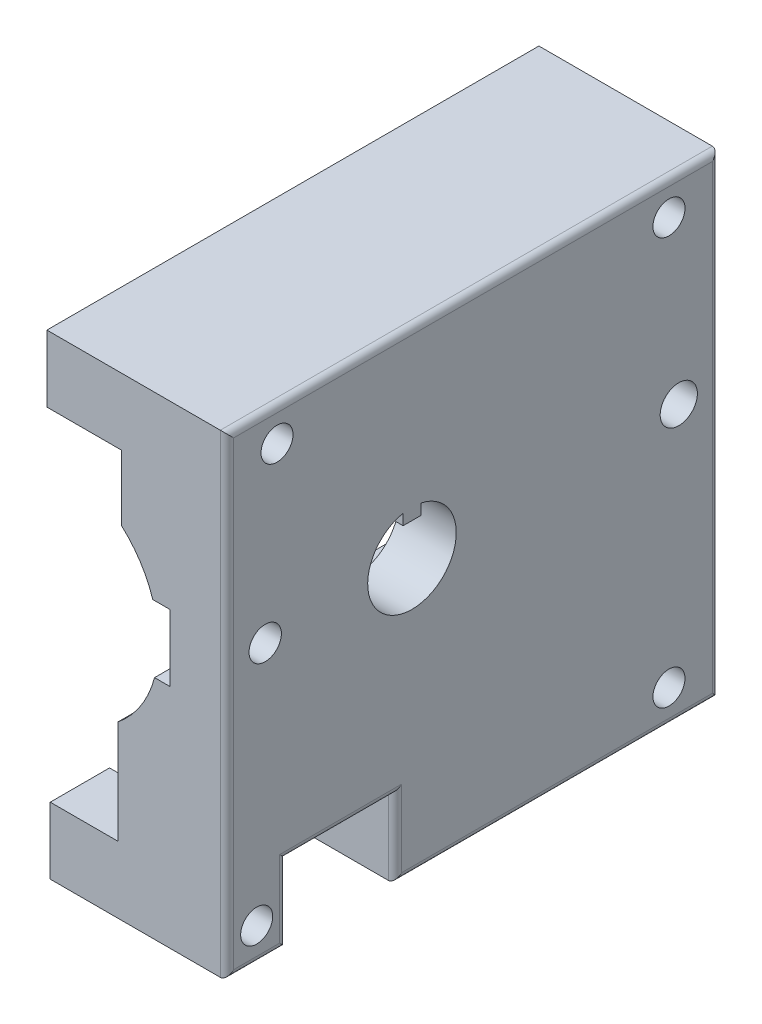
SolidWorks part; units mm, degrees
ref_plane "Front" through (0, 0, 0) normal (0, 0, 1) x (1, 0, 0)
ref_plane "Top" through (0, 0, 0) normal (0, 1, 0) x (1, 0, 0)
ref_plane "Right" through (0, 0, 0) normal (1, 0, 0) x (0, 0, -1)
sketch "Profile" plane through (0, 0, 0) normal (0, 0, 1) x (1, 0, 0)
  line L0 (-6.0107, -43.6279) -> (-6.0107, -33.6279)
  line L1 (-6.0107, -43.6279) -> (20.4893, -43.6279)
  line L2 (-6.5107, 17.4121) -> (-6.5107, 27.4121)
  line L3 (-6.5107, 27.4121) -> (20.4893, 27.4121)
  line L4 (20.4893, -43.6279) -> (20.4893, 27.4121)
  line L5 (-6.0107, -33.6279) -> (4.1393, -33.6279)
  line L6 (4.1393, -33.6279) -> (4.1393, -18.1379)
  line L7 (9.6313, -9.6379) -> (11.9493, -9.6379)
  line L8 (11.9493, -9.6379) -> (11.9493, 0.3621)
  line L9 (9.3593, 0.3621) -> (11.9493, 0.3621)
  line L10 (4.6393, 17.4121) -> (4.6393, 7.6371)
  line L11 (4.6393, 17.4121) -> (-6.5107, 17.4121)
  arc A0 (9.3593, 0.3621) -> (4.6393, 7.6371) centre (-6.1482, -4.5305) ccw
  arc A1 (4.1393, -18.1379) -> (9.6313, -9.6379) centre (-6.0948, -5.5013) ccw
  dimension "D14" = 16.261
  dimension "D17" = 16.261
  dimension "D2" = 10
  dimension "D3" = 2.59
  dimension "D4" = 2.318
  dimension "D5" = 9.775
  dimension "D6" = 11.15
  dimension "D7" = 15.49
  dimension "D8" = 10.15
  dimension "D9" = 10
  dimension "D10" = 26.5
  dimension "D11" = 71.04
  dimension "D12" = 27
  dimension "D13" = 10
  dimension "D15" = 23.99
  dimension "D16" = 5.492
extrude "ProfileExtrude" add sketch "Profile" along normal blind 73.76
sketch "HoseWindow" plane through (20.4893, 0, 0) normal (1, 0, 0) x (0, 0, -1)
  line L0 (-73.76, -43.6279) -> (0, -43.6279) construction
  line L1 (-64.87, -43.6279) -> (-48.58, -43.6279)
  line L2 (-64.87, -43.6279) -> (-64.87, -32.1279)
  line L3 (-64.87, -32.1279) -> (-48.58, -32.1279)
  line L4 (-48.58, -43.6279) -> (-48.58, -32.1279)
  line L5 (-73.76, -43.6279) -> (-73.76, 27.4121) construction
  dimension "D1" = 16.29
  dimension "D2" = 11.5
  dimension "D3" = 8.89
extrude "HoseWindowCut" cut sketch "HoseWindow" against normal through all
sketch "CageScrews" plane through (20.4893, 0, 0) normal (1, 0, 0) x (0, 0, -1)
  line L0 (-73.76, 27.4121) -> (0, 27.4121) construction
  line L1 (-73.76, -43.6279) -> (-73.76, 27.4121) construction
  line L2 (0, -43.6279) -> (0, 27.4121) construction
  line L3 (-48.58, -43.6279) -> (0, -43.6279) construction
  line L4 (-73.76, -43.6279) -> (-64.87, -43.6279) construction
  circle A0 centre (-66.26, 22.4121) radius 2.4
  circle A1 centre (-7.5, 22.4121) radius 2.4
  circle A2 centre (-7.5, -38.6279) radius 2.4
  circle A3 centre (-69.31, -38.6279) radius 2.4
  dimension "D1" = 4.8
  dimension "D2" = 4.8
  dimension "D3" = 4.8
  dimension "D4" = 4.8
  dimension "D5" = 5
  dimension "D6" = 7.5
  dimension "D7" = 7.5
  dimension "D8" = 5
  dimension "D9" = 5
  dimension "D10" = 7.5
  dimension "D11" = 5
  dimension "D12" = 4.45
extrude "CageScrewsCut" cut sketch "CageScrews" against normal through all
sketch "AxleHole" plane through (20.4893, 0, 0) normal (1, 0, 0) x (0, 0, -1)
  line L0 (-46.03, 2.3073) -> (-46.03, -9.2169) construction
  line L1 (-44.699, 2.3073) -> (-47.361, 2.3073)
  line L2 (-47.361, 2.3073) -> (-47.361, 3.9263)
  line L3 (-44.699, 2.3073) -> (-44.699, 3.9263)
  line L4 (-48.58, -43.6279) -> (0, -43.6279) construction
  line L5 (0, -43.6279) -> (0, 27.4121) construction
  arc A0 (-47.361, 3.9263) -> (-44.699, 3.9263) centre (-46.03, -2.5779) ccw
  dimension "D1" = 13.278
  dimension "D2" = 1.619
  dimension "D3" = 1.619
  dimension "D4" = 1.331
  dimension "D5" = 41.05
  dimension "D6" = 46.03
extrude "AxleHoleCut" cut sketch "AxleHole" against normal through all
sketch "SetScrews" plane through (20.4893, 0, 0) normal (1, 0, 0) x (0, 0, -1)
  line L0 (-46.03, -9.2169) -> (-46.03, -2.5779) construction
  circle A0 centre (-68.03, -2.5779) radius 2.4263
  circle A1 centre (-6.03, -2.5779) radius 2.7888
  arc A3 (-47.361, 3.9263) -> (-44.699, 3.9263) centre (-46.03, -2.5779) ccw construction
  dimension "D1" = 22
  dimension "D2" = 40
extrude "SetScrewsCut" cut sketch "SetScrews" against normal through all
fillet "Fillet1" radius 1 8 edges at (20.4893, -37.8779, 64.87) (20.4893, -37.8779, 48.58) (20.4893, -32.1279, 56.725) (20.4893, -43.6279, 69.315) (20.4893, -8.1079, 73.76) (20.4893, -43.6279, 24.29) (20.4893, -8.1079, 0) (20.4893, 27.4121, 36.88)
equation "\"BottomEdge\"=26.5mm"
equation "\"TopEdge\"=27mm"
equation "\"TotalHeight\"=71.04mm"
equation "\"TotalLength\"=73.76mm"
equation "\"Screw Clearance\" = 10mm"
equation "\"TopDepth\"= 11.15mm"
equation "\"BottomDepth\"=10.15mm"
equation "\"TopHeight\"=9.775mm"
equation "\"BottomHeight\"=15.49mm"
equation "\"TopChannelDepth\"=2.59mm"
equation "\"BottomChannelDepth\"=2.318mm"
equation "\"ChannelHeight\"=10mm"
equation "\"ChamberRadius\"=16.261mm"
equation "\"ChanRelHeight\"=23.99mm"
equation "\"ChanRelDepth\"=5.492mm"
equation "\"D2@Profile\"= \"ChannelHeight\""
equation "\"D4@Profile\"= \"BottomChannelDepth\""
equation "\"D3@Profile\"= \"TopChannelDepth\""
equation "\"D5@Profile\"= \"TopHeight\""
equation "\"D7@Profile\"= \"BottomHeight\""
equation "\"D9@Profile\"= \"Screw Clearance\""
equation "\"D13@Profile\"= \"Screw Clearance\""
equation "\"D8@Profile\"= \"BottomDepth\""
equation "\"D6@Profile\"= \"TopDepth\""
equation "\"D10@Profile\"= \"BottomEdge\""
equation "\"D12@Profile\"= \"TopEdge\""
equation "\"D11@Profile\"= \"TotalHeight\""
equation "\"D15@Profile\"= \"ChanRelHeight\""
equation "\"D16@Profile\"= \"ChanRelDepth\""
equation "\"D17@Profile\"= \"ChamberRadius\""
equation "\"D14@Profile\"= \"ChamberRadius\""
equation "\"D1@ProfileExtrude\"= \"TotalLength\""
equation "\"CageScrewDiameter\"=4.8mm"
equation "\"SetScrewDiameter\"=3.5mm"
equation "\"AxleRadius\"=6.639mm"
equation "\"KeyHeight\"=1.619mm"
equation "\"KeyWidth\"=2.662mm"
equation "\"HoseWindowWidth\"=16.29mm"
equation "\"HoseWindowHeight\"=11.5mm"
equation "\"HoseWindow-Edge\"=8.89mm"
equation "\"CageScrew-VerticalEdge\"=5.0mm"
equation "\"CageScrew-HorizontalEdge\"=7.5mm"
equation "\"CageScrew-HoseCornerScrewEdge\"=4.45mm"
equation "\"Axle-BottomEdge\"=41.05mm"
equation "\"Axle-FrontEdge\"=46.03mm"
equation "\"FrontSetScrew-Axel\"=40mm"
equation "\"D1@HoseWindow\"= \"HoseWindowWidth\""
equation "\"D2@HoseWindow\"= \"HoseWindowHeight\""
equation "\"D3@HoseWindow\"= \"HoseWindow-Edge\""
equation "\"D6@CageScrews\"= \"CageScrew-HorizontalEdge\""
equation "\"D7@CageScrews\"= \"CageScrew-HorizontalEdge\""
equation "\"D10@CageScrews\"= \"CageScrew-HorizontalEdge\""
equation "\"D12@CageScrews\"= \"CageScrew-HoseCornerScrewEdge\""
equation "\"D5@CageScrews\"= \"CageScrew-VerticalEdge\""
equation "\"D8@CageScrews\"= \"CageScrew-VerticalEdge\""
equation "\"D11@CageScrews\"= \"CageScrew-VerticalEdge\""
equation "\"D9@CageScrews\"= \"CageScrew-VerticalEdge\""
equation "\"D1@CageScrews\"= \"CageScrewDiameter\""
equation "\"D2@CageScrews\"= \"CageScrewDiameter\""
equation "\"D4@CageScrews\"= \"CageScrewDiameter\""
equation "\"D3@CageScrews\"= \"CageScrewDiameter\""
equation "\"D1@AxleHole\"= \"AxleRadius\" * 2"
equation "\"D3@AxleHole\"= \"KeyHeight\""
equation "\"D2@AxleHole\"= \"KeyHeight\""
equation "\"D4@AxleHole\"= \"KeyWidth\" / 2"
equation "\"D6@AxleHole\"= \"Axle-FrontEdge\""
equation "\"D5@AxleHole\"= \"Axle-BottomEdge\""
equation "\"D2@SetScrews\"= \"FrontSetScrew-Axel\""
equation "\"BackSetScrew-Axel\"=22mm"
equation "\"D1@SetScrews\"= \"BackSetScrew-Axel\""
